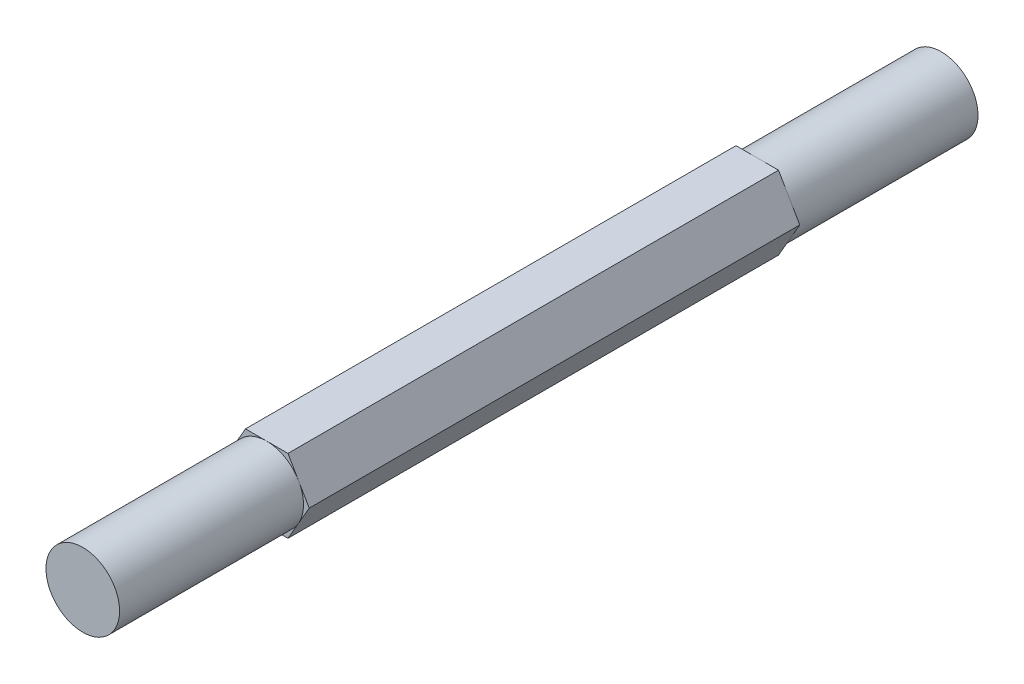
SolidWorks part; units mm, degrees
material "Plain Carbon Steel"
ref_plane "Front Plane" through (0, 0, 0) normal (0, 0, 1) x (1, 0, 0)
ref_plane "Top Plane" through (0, 0, 0) normal (0, 1, 0) x (1, 0, 0)
ref_plane "Right Plane" through (0, 0, 0) normal (1, 0, 0) x (0, 0, -1)
sketch "Sketch1" plane through (0, 0, 0) normal (0, 0, 1) x (1, 0, 0)
  line L1 (3.4641, 6) -> (-3.4641, 6)
  line L2 (-3.4641, 6) -> (-6.9282, 0)
  line L3 (-6.9282, 0) -> (-3.4641, -6)
  line L4 (-3.4641, -6) -> (3.4641, -6)
  line L5 (3.4641, -6) -> (6.9282, 0)
  line L6 (6.9282, 0) -> (3.4641, 6)
  circle A0 centre (0, 0) radius 6 construction
  dimension "D1" = 12
extrude "Boss-Extrude1" add sketch "Sketch1" along normal blind 80
sketch "Sketch2" plane through (0, 0, 80) normal (0, 0, 1) x (1, 0, 0)
  circle A0 centre (0, 0) radius 6
  dimension "D1" = 12
extrude "Boss-Extrude2" add sketch "Sketch2" along normal blind 30
sketch "Sketch3" plane through (0, 0, 0) normal (0, 0, -1) x (-1, 0, 0)
  circle A0 centre (0, 0) radius 6
  dimension "D1" = 12
extrude "Boss-Extrude3" add sketch "Sketch3" along normal blind 30
ref_plane "Plane1" through (0, 0, 40) normal (0, 0, -1) x (-1, 0, 0)
